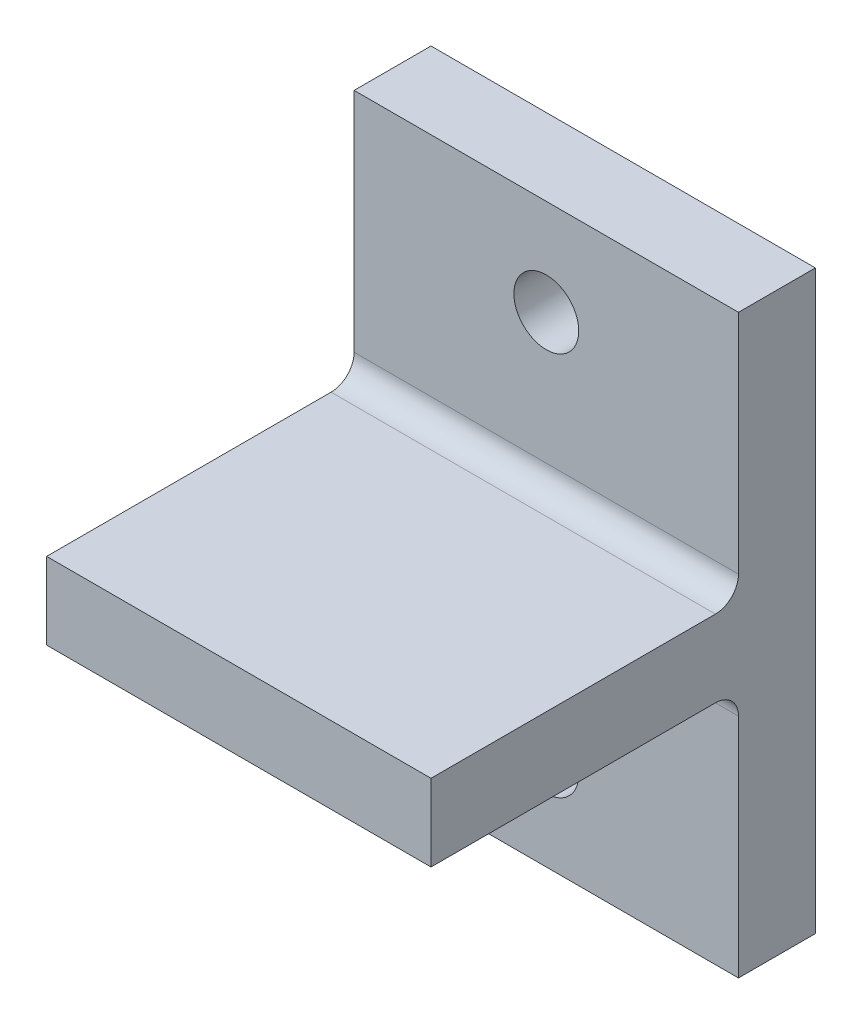
SolidWorks part; units mm, degrees
ref_plane "Alzado" through (0, 0, 0) normal (0, 0, 1) x (1, 0, 0)
ref_plane "Planta" through (0, 0, 0) normal (0, 1, 0) x (1, 0, 0)
ref_plane "Vista lateral" through (0, 0, 0) normal (1, 0, 0) x (0, 0, -1)
sketch "Croquis1" plane through (0, 0, 0) normal (0, 0, 1) x (1, 0, 0)
  line L1 (-25, -37.5) -> (25, -37.5)
  line L2 (-25, -37.5) -> (-25, 37.5)
  line L3 (-25, 37.5) -> (25, 37.5)
  line L4 (25, -37.5) -> (25, 37.5)
  line L5 (-25, -37.5) -> (25, 37.5) construction
  line L6 (-25, 37.5) -> (25, -37.5) construction
  point P0 (0, 0)
  dimension "D1" = 50
  dimension "D2" = 75
extrude "Saliente-Extruir1" add sketch "Croquis1" along normal blind 10
sketch "Croquis2" plane through (0, 0, 10) normal (0, 0, 1) x (1, 0, 0)
  line L0 (25, -37.5) -> (25, 37.5) construction
  line L1 (-25, -5) -> (25, -5)
  line L2 (-25, -5) -> (-25, 5)
  line L3 (-25, 5) -> (25, 5)
  line L4 (25, -5) -> (25, 5)
  line L5 (-25, -5) -> (25, 5) construction
  line L6 (-25, 5) -> (25, -5) construction
  point P0 (0, 0)
  dimension "D1" = 10
extrude "Saliente-Extruir2" add sketch "Croquis2" along normal blind 40
fillet "Redondeo1" radius 3 2 edges
sketch "Croquis3" plane through (0, 0, 0) normal (0, 0, -1) x (-1, 0, 0)
  line L0 (0, 0) -> (34.9273, 0) construction
  line L1 (-25, 37.5) -> (25, 37.5) construction
  point P0 (0, 25)
  point P4 (0, -25)
  point P5 (0, 37.5)
  dimension "D1" = 50
hole_wizard "Taladro de margen para 5/161" positions "Croquis3D1" profile "Croquis5" hole size "5/16" standard "Ansi Inch" end condition through all
sketch3d "Croquis3D1"
  point P0 (0, 25, 0)
  point P3 (0, -25, 0)
sketch "Croquis5" plane through (0, 25, 0) normal (1, 0, 0) x (0, 1, 0)
  line L0 (0, 0) -> (0, 50)
  line L1 (0, 50) -> (4.2164, 50)
  line L2 (4.2164, 50) -> (4.2164, 0)
  line L5 (4.2164, 0) -> (0, 0)
  line L11 (0, -6.35) -> (0, 107.95) construction
  dimension "Diámetro de taladro hasta el siguiente" = 8.4328
  dimension "Profundidad de taladro hasta el siguiente" = 50
